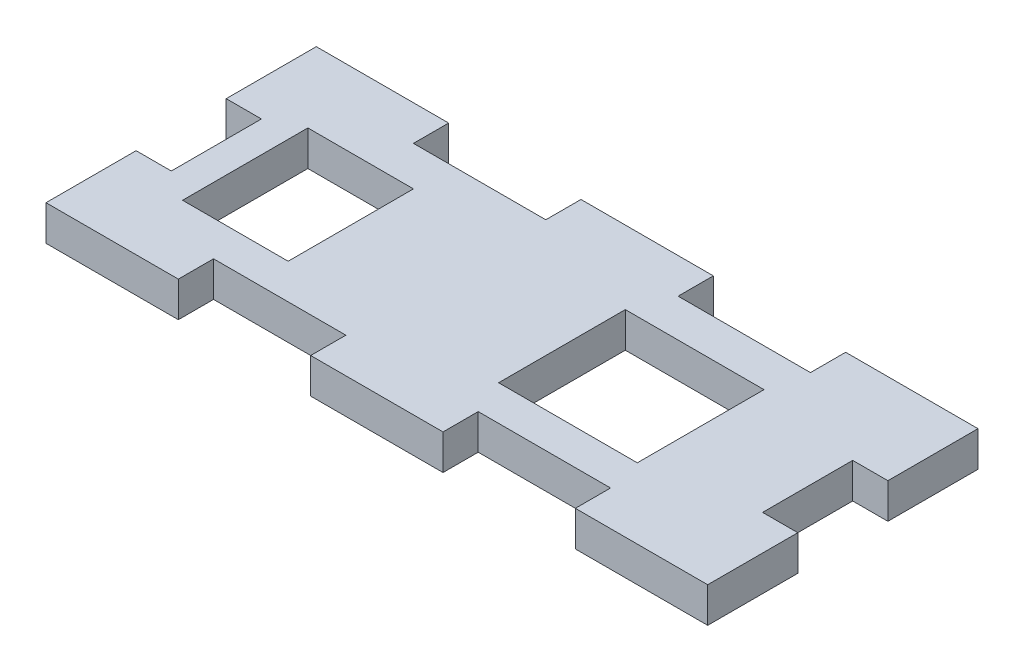
SolidWorks part; units mm, degrees
ref_plane "Front Plane" through (0, 0, 0) normal (0, 0, 1) x (1, 0, 0)
ref_plane "Top Plane" through (0, 0, 0) normal (0, 1, 0) x (1, 0, 0)
ref_plane "Right Plane" through (0, 0, 0) normal (1, 0, 0) x (0, 0, -1)
sketch "Sketch1" plane through (0, 0, 0) normal (0, 1, 0) x (1, 0, 0)
  line L1 (-29.845, -12.192) -> (29.845, -12.192)
  line L2 (-29.845, -12.192) -> (-29.845, 12.192)
  line L3 (-29.845, 12.192) -> (29.845, 12.192)
  line L4 (29.845, -12.192) -> (29.845, 12.192)
  line L5 (-29.845, -12.192) -> (29.845, 12.192) construction
  line L6 (-29.845, 12.192) -> (29.845, -12.192) construction
  point P0 (0, 0)
  dimension "D1" = 59.69
  dimension "D2" = 24.384
extrude "Boss-Extrude2" add sketch "Sketch1" along normal blind 3.175
sketch "Sketch3" plane through (0, 3.175, 0) normal (0, 1, 0) x (1, 0, 0)
  line L0 (29.845, 12.192) -> (-29.845, 12.192) construction
  line L1 (-5.969, 9.017) -> (5.969, 9.017) construction
  line L2 (-5.969, 9.017) -> (-5.969, 15.367) construction
  line L3 (-5.969, 15.367) -> (5.969, 15.367) construction
  line L4 (5.969, 9.017) -> (5.969, 15.367) construction
  line L5 (-5.969, 9.017) -> (5.969, 15.367) construction
  line L6 (-5.969, 15.367) -> (5.969, 9.017) construction
  line L7 (-29.845, -12.192) -> (29.845, -12.192) construction
  line L8 (5.969, 9.017) -> (17.907, 9.017)
  line L9 (5.969, 9.017) -> (5.969, 12.192)
  line L10 (5.969, 12.192) -> (17.907, 12.192)
  line L11 (17.907, 9.017) -> (17.907, 12.192)
  line L12 (5.969, -12.192) -> (17.907, -12.192)
  line L13 (5.969, -12.192) -> (5.969, -9.017)
  line L14 (5.969, -9.017) -> (17.907, -9.017)
  line L15 (17.907, -12.192) -> (17.907, -9.017)
  point P0 (0, 12.192)
  dimension "D1" = 6.35
  dimension "D2" = 11.938
  dimension "D3" = 11.938
  dimension "D4" = 3.175
extrude "Cut-Extrude2" cut sketch "Sketch3" against normal blind 3.175
pattern_linear "LPattern2" count 2 spacing 23.876 along (-1, 0, 0) of "Cut-Extrude2"
sketch "Sketch4" plane through (0, 3.175, 0) normal (0, 1, 0) x (1, 0, 0)
  line L0 (-29.845, 12.192) -> (-29.845, -12.192) construction
  line L1 (-33.02, -4.064) -> (-26.67, -4.064)
  line L2 (-33.02, -4.064) -> (-33.02, 4.064)
  line L3 (-33.02, 4.064) -> (-26.67, 4.064)
  line L4 (-26.67, -4.064) -> (-26.67, 4.064)
  line L5 (-33.02, -4.064) -> (-26.67, 4.064) construction
  line L6 (-33.02, 4.064) -> (-26.67, -4.064) construction
  line L8 (29.845, -12.192) -> (29.845, 12.192) construction
  line L9 (26.67, -4.064) -> (33.02, -4.064)
  line L10 (26.67, -4.064) -> (26.67, 4.064)
  line L11 (26.67, 4.064) -> (33.02, 4.064)
  line L12 (33.02, -4.064) -> (33.02, 4.064)
  line L13 (26.67, -4.064) -> (33.02, 4.064) construction
  line L14 (26.67, 4.064) -> (33.02, -4.064) construction
  point P0 (-29.845, 0)
  point P7 (29.845, 0)
  dimension "D1" = 8.128
  dimension "D2" = 6.35
  dimension "D3" = 6.35
extrude "Cut-Extrude3" cut sketch "Sketch4" against normal blind 3.175
sketch "Sketch5" plane through (0, 3.175, 0) normal (0, 1, 0) x (1, 0, 0)
  line L0 (-17.907, -9.017) -> (17.907, -9.017) construction
  line L2 (-26.67, -9.017) -> (26.67, -9.017) construction
  line L3 (-26.67, -9.017) -> (-26.67, 9.017) construction
  line L4 (-26.67, 9.017) -> (26.67, 9.017) construction
  line L5 (26.67, -9.017) -> (26.67, 9.017) construction
  line L6 (-26.67, -9.017) -> (26.67, 9.017) construction
  line L7 (-26.67, 9.017) -> (26.67, -9.017) construction
  line L8 (-26.67, -9.017) -> (-23.876, -9.017) construction
  line L9 (-26.67, -9.017) -> (-26.67, -5.842) construction
  line L10 (-26.67, -5.842) -> (-23.876, -5.842) construction
  line L11 (-23.876, -9.017) -> (-23.876, -5.842) construction
  line L12 (-23.876, -5.842) -> (-14.351, -5.842)
  line L13 (-23.876, -5.842) -> (-23.876, 5.461)
  line L14 (-23.876, 5.461) -> (-14.351, 5.461)
  line L15 (-14.351, -5.842) -> (-14.351, 5.461)
  line L16 (26.67, -9.017) -> (17.145, -9.017) construction
  line L17 (26.67, -9.017) -> (26.67, -5.842) construction
  line L18 (26.67, -5.842) -> (17.145, -5.842) construction
  line L19 (17.145, -9.017) -> (17.145, -5.842) construction
  line L20 (17.145, -5.842) -> (4.6355, -5.842)
  line L21 (17.145, -5.842) -> (17.145, 5.588)
  line L22 (17.145, 5.588) -> (4.6355, 5.588)
  line L23 (4.6355, -5.842) -> (4.6355, 5.588)
  point P1 (0, 0)
  dimension "D1" = 18.034
  dimension "D2" = 53.34
  dimension "D3" = 2.794
  dimension "D4" = 3.175
  dimension "D5" = 9.525
  dimension "D6" = 11.303
  dimension "D7" = 9.525
  dimension "D8" = 12.5095
  dimension "D9" = 11.43
extrude "Cut-Extrude4" cut sketch "Sketch5" against normal blind 3.175
